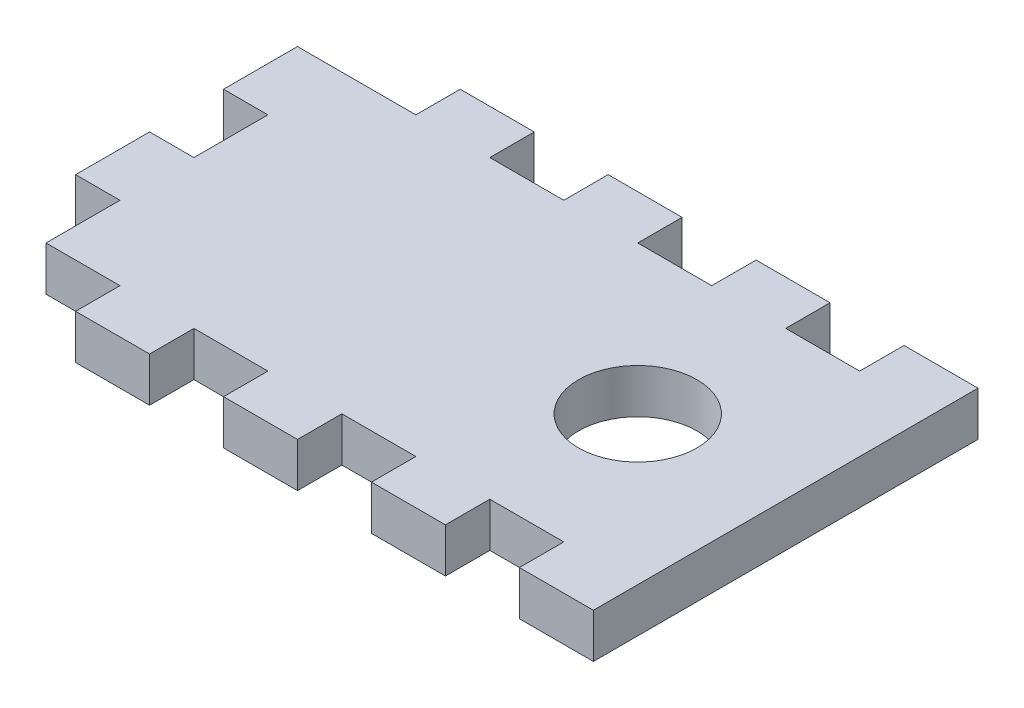
SolidWorks part; units mm, degrees
ref_plane "Front Plane" through (0, 0, 0) normal (0, 0, 1) x (1, 0, 0)
ref_plane "Top Plane" through (0, 0, 0) normal (0, 1, 0) x (1, 0, 0)
ref_plane "Right Plane" through (0, 0, 0) normal (1, 0, 0) x (0, 0, -1)
sketch "Sketch1" plane through (0, 0, 0) normal (0, 1, 0) x (1, 0, 0)
  line L1 (-20, 13) -> (20, 13)
  line L2 (-20, 13) -> (-20, -13)
  line L3 (-20, -13) -> (20, -13)
  line L4 (20, 13) -> (20, -13)
  line L5 (-20, 13) -> (20, -13) construction
  line L6 (-20, -13) -> (20, 13) construction
  point P0 (0, 0)
  dimension "D1" = 40
  dimension "D2" = 26
extrude "Boss-Extrude1" add sketch "Sketch1" along normal mid plane 3
sketch "Sketch2" plane through (0, -1.5, 0) normal (0, -1, 0) x (1, 0, 0)
  circle A0 centre (10, 0) radius 4
  dimension "D1" = 8
  dimension "D2" = 10
extrude "Cut-Extrude1" cut sketch "Sketch2" against normal up to surface (3 mm away) up to face at (0, 1.5, 0)
sketch "Sketch8" plane through (-20, 0, 0) normal (-1, 0, 0) x (0, 0, 1)
  line L0 (-13, -1.5) -> (13, -1.5) construction
  line L1 (-13, 1.5) -> (-10, 1.5)
  line L2 (-13, 1.5) -> (-13, -1.5)
  line L3 (-13, -1.5) -> (-10, -1.5)
  line L4 (-10, 1.5) -> (-10, -1.5)
  line L6 (13, 1.5) -> (10, 1.5)
  line L7 (13, 1.5) -> (13, -1.5)
  line L8 (13, -1.5) -> (10, -1.5)
  line L9 (10, 1.5) -> (10, -1.5)
  line L10 (-10, 1.5) -> (-5, 1.5)
  line L11 (-10, 1.5) -> (-10, -1.5)
  line L12 (-10, -1.5) -> (-5, -1.5)
  line L13 (-5, 1.5) -> (-5, -1.5)
  line L18 (5, 1.5) -> (10, 1.5)
  line L19 (5, 1.5) -> (5, -1.5)
  line L20 (5, -1.5) -> (10, -1.5)
  line L21 (10, 1.5) -> (10, -1.5)
  line L22 (-5, 1.5) -> (0, 1.5)
  line L23 (-5, 1.5) -> (-5, -1.5)
  line L24 (-5, -1.5) -> (0, -1.5)
  line L25 (0, 1.5) -> (0, -1.5)
  line L26 (0, 1.5) -> (5, 1.5)
  line L27 (0, 1.5) -> (0, -1.5)
  line L28 (0, -1.5) -> (5, -1.5)
  line L29 (5, 1.5) -> (5, -1.5)
  line M12 (-13, -1.5) -> (13, -1.5)
  line M14 (13, 1.5) -> (-13, 1.5)
  dimension "D1" = 3
extrude "Boss-Extrude7" add sketch "Sketch8" along normal blind 3 contours L13 L4 M14 M12 | L25 L19 M14 M12
sketch "Sketch9" plane through (0, -1.5, 0) normal (0, -1, 0) x (1, 0, 0)
  line L0 (-23, -10) -> (-20, -10) construction
  line L1 (-20, -13) -> (-15, -13)
  line L2 (-20, -13) -> (-20, -10)
  line L3 (-20, -10) -> (-15, -10)
  line L4 (-15, -13) -> (-15, -10)
  line L5 (0, 0) -> (-5.3473, 0) construction
  line L6 (-15, -13) -> (-10, -13)
  line L7 (-15, -13) -> (-15, -10)
  line L8 (-15, -10) -> (-10, -10)
  line L9 (-10, -13) -> (-10, -10)
  line L10 (-10, -13) -> (-5, -13)
  line L11 (-10, -13) -> (-10, -10)
  line L12 (-10, -10) -> (-5, -10)
  line L13 (-5, -13) -> (-5, -10)
  line L14 (-10, 10) -> (-5, 10)
  line L15 (-5, 13) -> (-5, 10)
  line L16 (-10, 13) -> (-5, 13)
  line L17 (-10, 13) -> (-10, 10)
  line L18 (-15, 10) -> (-10, 10)
  line L19 (-10, 13) -> (-10, 10)
  line L20 (-15, 13) -> (-10, 13)
  line L21 (-15, 13) -> (-15, 10)
  line L22 (-20, 10) -> (-15, 10)
  line L23 (-15, 13) -> (-15, 10)
  line L24 (-20, 13) -> (-15, 13)
  line L25 (-20, 13) -> (-20, 10)
  line L26 (15, 10) -> (20, 10)
  line L27 (-5, -13) -> (0, -13)
  line L28 (-5, -13) -> (-5, -10)
  line L29 (-5, -10) -> (0, -10)
  line L30 (0, -13) -> (0, -10)
  line L31 (0, -13) -> (5, -13)
  line L32 (0, -13) -> (0, -10)
  line L33 (0, -10) -> (5, -10)
  line L34 (5, -13) -> (5, -10)
  line L35 (5, -13) -> (10, -13)
  line L36 (5, -13) -> (5, -10)
  line L37 (5, -10) -> (10, -10)
  line L38 (10, -13) -> (10, -10)
  line L39 (10, -13) -> (15, -13)
  line L40 (10, -13) -> (10, -10)
  line L41 (10, -10) -> (15, -10)
  line L42 (15, -13) -> (15, -10)
  line L43 (15, -13) -> (20, -13)
  line L44 (15, -13) -> (15, -10)
  line L45 (15, -10) -> (20, -10)
  line L46 (20, -13) -> (20, -10)
  line L47 (20, 13) -> (20, 10)
  line L48 (15, 13) -> (20, 13)
  line L49 (15, 13) -> (15, 10)
  line L50 (10, 10) -> (15, 10)
  line L51 (15, 13) -> (15, 10)
  line L52 (10, 13) -> (15, 13)
  line L53 (10, 13) -> (10, 10)
  line L54 (5, 10) -> (10, 10)
  line L55 (10, 13) -> (10, 10)
  line L56 (5, 13) -> (10, 13)
  line L57 (5, 13) -> (5, 10)
  line L58 (0, 10) -> (5, 10)
  line L59 (5, 13) -> (5, 10)
  line L60 (0, 13) -> (5, 13)
  line L61 (0, 13) -> (0, 10)
  line L62 (-5, 10) -> (0, 10)
  line L63 (0, 13) -> (0, 10)
  line L64 (-5, 13) -> (0, 13)
  line L65 (-5, 13) -> (-5, 10)
  line M11 (20, 13) -> (-20, 13)
  line M12 (-20, 13) -> (-20, 5)
  line M20 (-20, -10) -> (-20, -13)
  line M21 (-20, -13) -> (20, -13)
  dimension "D1" = 5
extrude "Cut-Extrude2" cut sketch "Sketch9" against normal up to surface (3 mm away) contours L4 L3 M21 M20 | L13 L12 L9 M21 | L22 L21 M12 M11 | L17 L14 L15 M11 | L61 L58 L57 M11 | L53 L50 L49 M11 | L32 L31 L34 L33 | L40 L39 L42 L41
